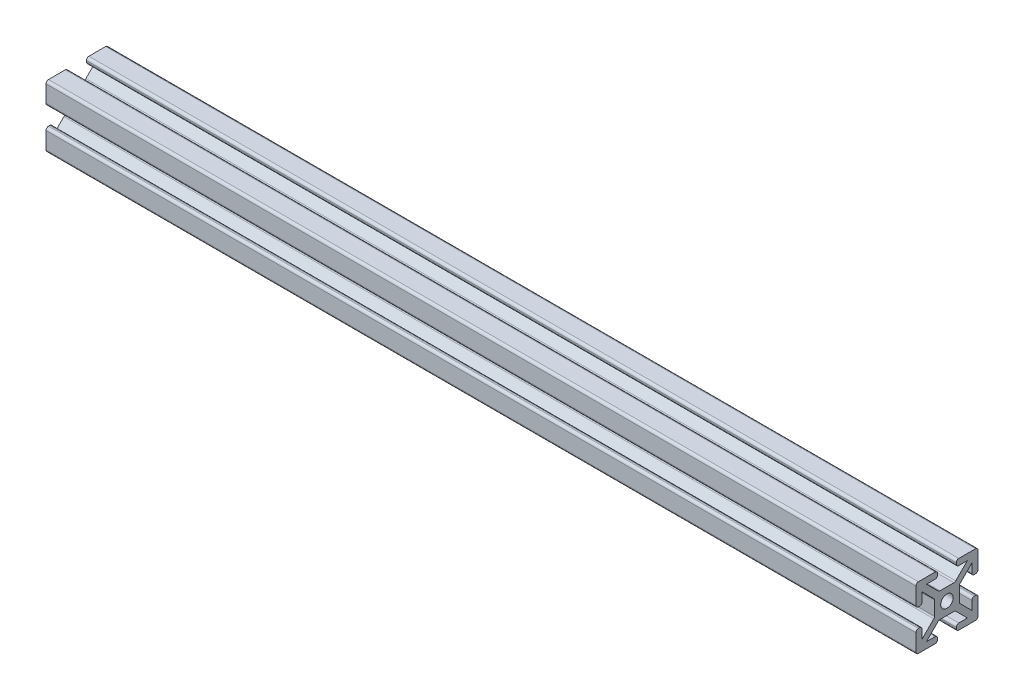
SolidWorks part; units mm, degrees
material "1060 Alloy"
ref_plane "Front Plane" through (0, 0, 0) normal (0, 0, 1) x (1, 0, 0)
ref_plane "Top Plane" through (0, 0, 0) normal (0, 1, 0) x (1, 0, 0)
ref_plane "Right Plane" through (0, 0, 0) normal (1, 0, 0) x (0, 0, -1)
sketch "Sketch1" plane through (0, 0, 0) normal (0, 1, 0) x (1, 0, 0)
  line L0 (0, 0) -> (280, 0)
other "Size 4X4 (1)"
ref_plane "Plane1" through (0, 0, 0) normal (1, 0, 0) x (0, 0, -1)
sketch "Sketch11" plane through (0, 0, 0) normal (1, 0, 0) x (0, 0, -1)
  line L0 (-3, 9.2) -> (-3, 8.8)
  line L1 (-2.2544, 4) -> (2.2544, 4)
  line L2 (-4, 2.2544) -> (-4, -2.2544)
  line L3 (-2.2544, -4) -> (2.2544, -4)
  line L4 (4, 2.2544) -> (4, -2.2544)
  line L7 (-6.5858, 8) -> (-3.8, 8)
  line L8 (-8, 6.5858) -> (-8, 3.8)
  line L9 (-6.5858, -8) -> (-3.8, -8)
  line L10 (8, 6.5858) -> (8, 3.8)
  line L12 (9.7657, -9.7657) -> (10, -10) construction
  line L13 (-9.2, 10) -> (-3.8, 10)
  line L14 (-10, 9.2) -> (-10, 3.8)
  line L15 (-9.2, -10) -> (-3.8, -10)
  line L16 (10, 9.2) -> (10, 3.8)
  line L17 (-10, 10) -> (-9.7657, 9.7657) construction
  line L18 (-10, -10) -> (-9.7657, -9.7657) construction
  line L21 (3, 9.2) -> (3, 8.8)
  line L22 (3, -9.2) -> (3, -8.8)
  line L23 (-3, -9.2) -> (-3, -8.8)
  line L24 (3.8, 10) -> (9.2, 10)
  line L25 (3.8, 8) -> (6.5858, 8)
  line L26 (-9.2, 3) -> (-8.8, 3)
  line L27 (9.2, 3) -> (8.8, 3)
  line L28 (9.2, -3) -> (8.8, -3)
  line L29 (-9.2, -3) -> (-8.8, -3)
  line L30 (-10, -3.8) -> (-10, -9.2)
  line L31 (-8, -3.8) -> (-8, -6.5858)
  line L32 (8, -3.8) -> (8, -6.5858)
  line L33 (10, -3.8) -> (10, -9.2)
  line L34 (3.8, -8) -> (6.5858, -8)
  line L35 (3.8, -10) -> (9.2, -10)
  line L36 (6.5858, 8) -> (2.8201, 4.2343)
  line L37 (8, 6.5858) -> (4.2343, 2.8201)
  line L38 (8, -6.5858) -> (4.2343, -2.8201)
  line L39 (6.5858, -8) -> (2.8201, -4.2343)
  line L40 (-6.5858, -8) -> (-2.8201, -4.2343)
  line L41 (-8, -6.5858) -> (-4.2343, -2.8201)
  line L42 (-8, 6.5858) -> (-4.2343, 2.8201)
  line L43 (-6.5858, 8) -> (-2.8201, 4.2343)
  line L47 (9.7657, 9.7657) -> (10, 10) construction
  circle A0 centre (0, 0) radius 2
  arc A1 (9.2, -3) -> (10, -3.8) centre (9.2, -3.8) cw
  arc A2 (8.8, -3) -> (8, -3.8) centre (8.8, -3.8) ccw
  arc A3 (3, -9.2) -> (3.8, -10) centre (3.8, -9.2) ccw
  arc A4 (3, -8.8) -> (3.8, -8) centre (3.8, -8.8) cw
  arc A5 (-3, -9.2) -> (-3.8, -10) centre (-3.8, -9.2) cw
  arc A6 (-3, -8.8) -> (-3.8, -8) centre (-3.8, -8.8) ccw
  arc A7 (-8.8, -3) -> (-8, -3.8) centre (-8.8, -3.8) cw
  arc A8 (-9.2, -3) -> (-10, -3.8) centre (-9.2, -3.8) ccw
  arc A9 (-10, -9.2) -> (-9.2, -10) centre (-9.2, -9.2) ccw
  arc A10 (9.2, -10) -> (10, -9.2) centre (9.2, -9.2) ccw
  arc A11 (9.2, 10) -> (10, 9.2) centre (9.2, 9.2) cw
  arc A12 (-9.2, 10) -> (-10, 9.2) centre (-9.2, 9.2) ccw
  arc A13 (9.2, 3) -> (10, 3.8) centre (9.2, 3.8) ccw
  arc A14 (8.8, 3) -> (8, 3.8) centre (8.8, 3.8) cw
  arc A15 (3, 9.2) -> (3.8, 10) centre (3.8, 9.2) cw
  arc A16 (3, 8.8) -> (3.8, 8) centre (3.8, 8.8) ccw
  arc A17 (-3, 9.2) -> (-3.8, 10) centre (-3.8, 9.2) ccw
  arc A18 (-3, 8.8) -> (-3.8, 8) centre (-3.8, 8.8) cw
  arc A19 (-8.8, 3) -> (-8, 3.8) centre (-8.8, 3.8) ccw
  arc A20 (-9.2, 3) -> (-10, 3.8) centre (-9.2, 3.8) cw
  arc A21 (-2.8201, 4.2343) -> (-2.2544, 4) centre (-2.2544, 4.8) ccw
  arc A22 (4.2343, 2.8201) -> (4, 2.2544) centre (4.8, 2.2544) ccw
  arc A23 (2.8201, 4.2343) -> (2.2544, 4) centre (2.2544, 4.8) cw
  arc A24 (4.2343, -2.8201) -> (4, -2.2544) centre (4.8, -2.2544) cw
  arc A25 (2.8201, -4.2343) -> (2.2544, -4) centre (2.2544, -4.8) ccw
  arc A26 (-2.8201, -4.2343) -> (-2.2544, -4) centre (-2.2544, -4.8) cw
  arc A27 (-4.2343, -2.8201) -> (-4, -2.2544) centre (-4.8, -2.2544) ccw
  arc A28 (-4.2343, 2.8201) -> (-4, 2.2544) centre (-4.8, 2.2544) cw
  point P7 (0, 0)
  point P10 (-2.5858, 4)
  point P53 (10, -3)
  point P56 (8, -3)
  point P59 (3, -10)
  point P62 (3, -8)
  point P65 (-3, -10)
  point P68 (-3, -8)
  point P71 (-8, -3)
  point P74 (-10, -3)
  point P89 (10, 3)
  point P92 (8, 3)
  point P95 (3, 10)
  point P98 (3, 8)
  point P101 (-3, 10)
  point P104 (-3, 8)
  point P107 (-8, 3)
  point P110 (-10, 3)
  point P116 (4, 2.5858)
  point P119 (2.5858, 4)
  point P122 (4, -2.5858)
  point P125 (2.5858, -4)
  point P128 (-2.5858, -4)
  point P131 (-4, -2.5858)
  point P134 (-4, 2.5858)
  dimension "D3" = 4
  dimension "D11" = 0.8
  dimension "D12" = 0.8
  dimension "D2" = 0.8
  dimension "D4" = 20
  dimension "D6" = 20
  dimension "D8" = 7
  dimension "D9" = 7
